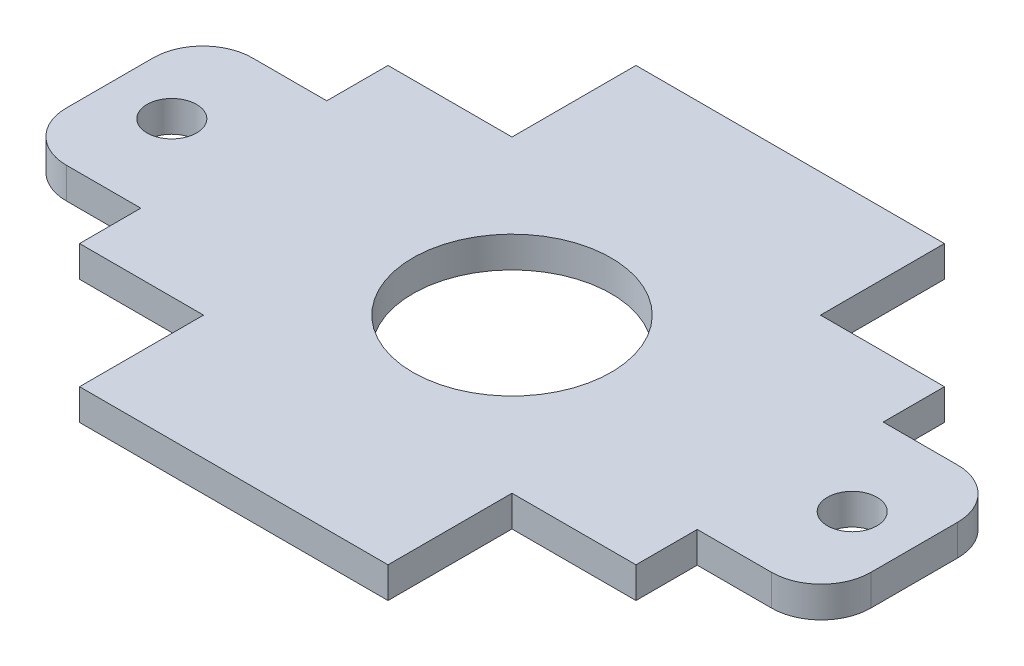
SolidWorks part; units mm, degrees
ref_plane "Front Plane" through (0, 0, 0) normal (0, 0, 1) x (1, 0, 0)
ref_plane "Top Plane" through (0, 0, 0) normal (0, 1, 0) x (1, 0, 0)
ref_plane "Right Plane" through (0, 0, 0) normal (1, 0, 0) x (0, 0, -1)
sketch "Sketch1" plane through (0, 0, 0) normal (0, 1, 0) x (1, 0, 0)
  line L5 (15.8, 15.8) -> (-15.8, -15.8) construction
  line L6 (-28.5, 15.8) -> (-28.5, 9.525)
  line L15 (-28.5, -9.525) -> (-36.12, -9.525)
  line L17 (-28.5, 9.525) -> (-36.12, 9.525)
  line L18 (-41.2, -4.445) -> (-41.2, 4.445)
  line L19 (-15.8, 28.5) -> (15.8, 28.5)
  line L20 (15.8, -28.5) -> (-15.8, -28.5)
  line L22 (15.8, -15.8) -> (-15.8, 15.8) construction
  line L23 (0, -28.5) -> (0, 28.5) construction
  line L24 (28.5, -9.525) -> (36.12, -9.525)
  line L25 (41.2, -4.445) -> (41.2, 4.445)
  line L26 (28.5, 9.525) -> (36.12, 9.525)
  line L29 (-15.8, 15.8) -> (-28.5, 15.8)
  line L30 (-15.8, 15.8) -> (-15.8, 28.5)
  line L35 (15.8, 15.8) -> (28.5, 15.8)
  line L36 (15.8, 15.8) -> (15.8, 28.5)
  line L39 (-28.5, -9.525) -> (-28.5, -15.8)
  line L40 (28.5, 15.8) -> (28.5, 9.525)
  line L41 (15.8, -15.8) -> (28.5, -15.8)
  line L42 (15.8, -15.8) -> (15.8, -28.5)
  line L45 (28.5, -9.525) -> (28.5, -15.8)
  line L47 (-15.8, -15.8) -> (-28.5, -15.8)
  line L48 (-15.8, -15.8) -> (-15.8, -28.5)
  circle A0 centre (0, 0) radius 10.16
  circle A13 centre (-34.85, 0) radius 2.54
  arc A14 (36.12, -9.525) -> (41.2, -4.445) centre (36.12, -4.445) ccw
  arc A15 (41.2, 4.445) -> (36.12, 9.525) centre (36.12, 4.445) ccw
  arc A16 (-36.12, 9.525) -> (-41.2, 4.445) centre (-36.12, 4.445) ccw
  arc A17 (-36.12, -9.525) -> (-41.2, -4.445) centre (-36.12, -4.445) cw
  circle A18 centre (34.85, 0) radius 2.54
  point P9 (-28.5, 0)
  point P38 (0, 0)
  point P55 (41.2, -9.525)
  point P58 (41.2, 9.525)
  dimension "D4" = 12.7
  dimension "D5" = 20.32
  dimension "D6" = 12.7
  dimension "D10" = 6.35
  dimension "D12" = 5.08
  dimension "D13" = 5.08
  dimension "D2" = 12.7
  dimension "D3" = 82.4
  dimension "D7" = 12.7
  dimension "D9" = 19.05
  dimension "D11" = 9.525
  dimension "D8" = 12.7
  dimension "D14" = 12.7
  dimension "D15" = 0
extrude "Boss-Extrude1" add sketch "Sketch1" along normal blind 3.175
